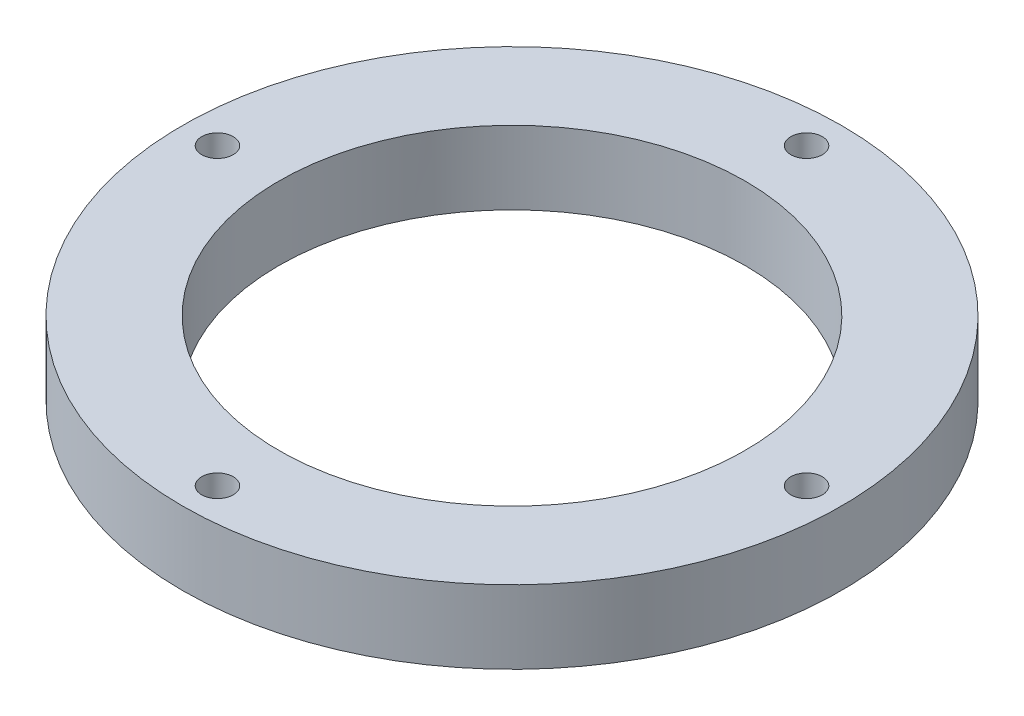
SolidWorks part; units mm, degrees
ref_plane "Front Plane" through (0, 0, 0) normal (0, 0, 1) x (1, 0, 0)
ref_plane "Top Plane" through (0, 0, 0) normal (0, 1, 0) x (1, 0, 0)
ref_plane "Right Plane" through (0, 0, 0) normal (1, 0, 0) x (0, 0, -1)
sketch "Sketch2" plane through (0, 0, 0) normal (0, 1, 0) x (1, 0, 0)
  circle A0 centre (0, 0) radius 45
  dimension "D1" = 90
extrude "Boss-Extrude1" add sketch "Sketch2" against normal blind 10
sketch "Sketch7" plane through (0, -10, 0) normal (0, -1, 0) x (-1, 0, 0)
  circle A0 centre (0, 0) radius 31.85
  dimension "D1" = 63.7
extrude "Cut-Extrude1" cut sketch "Sketch7" against normal through all both and the other way through all
sketch "Sketch8" plane through (0, -10, 0) normal (0, -1, 0) x (1, 0, 0)
  line L0 (0, -40.22) -> (0, 40.22) construction
  line L1 (40.22, 0) -> (-40.22, 0) construction
  circle A0 centre (0, 0) radius 40.22 construction
  circle A1 centre (-40.22, 0) radius 2.15
  circle A2 centre (0, -40.22) radius 2.15
  circle A3 centre (0, 40.22) radius 2.15
  circle A4 centre (40.22, 0) radius 2.15
extrude "Cut-Extrude2" cut sketch "Sketch8" against normal through all
sketch "Sketch9" plane through (0, -10, 0) normal (0, -1, 0) x (-1, 0, 0)
  circle A0 centre (40.22, 0) radius 4
  circle A1 centre (0, 40.22) radius 4
  circle A2 centre (-40.22, 0) radius 4
  circle A3 centre (0, -40.22) radius 4
extrude "Cut-Extrude3" [suppressed] cut sketch "Sketch9" against normal blind 4
sketch3d "3DSketch2"
  line L0 (0, 0, 0) -> (32.0557, 0, -31.5822) construction
  line L2 (0, 0, 0) -> (0, 0, -36.1869) construction
  point P1 (0, 0, 0)
